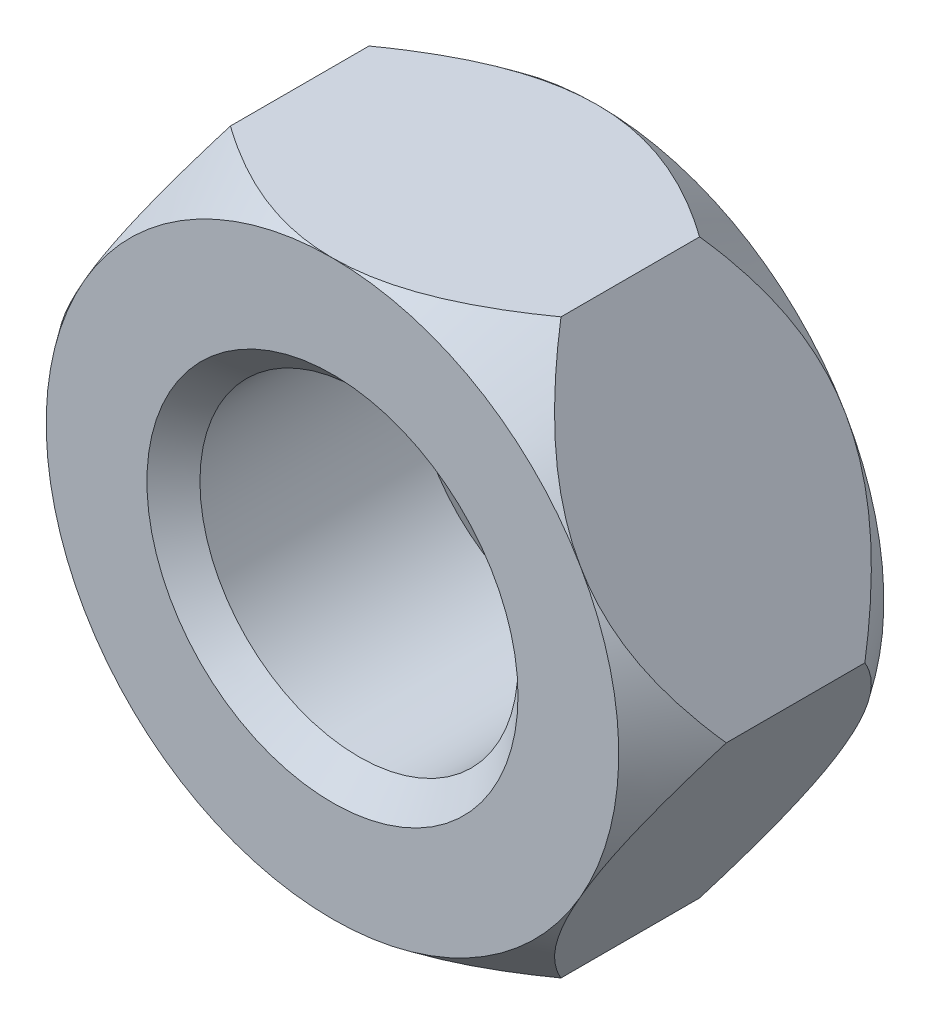
SolidWorks part; units mm, degrees
ref_plane "Plano frontal" through (0, 0, 0) normal (0, 0, 1) x (1, 0, 0)
ref_plane "Plano superior" through (0, 0, 0) normal (0, 1, 0) x (1, 0, 0)
ref_plane "Plano direito" through (0, 0, 0) normal (1, 0, 0) x (0, 0, -1)
sketch "Esboço2" plane through (0, 0, 0) normal (0, 0, 1) x (1, 0, 0)
  line L1 (3.1177, 0) -> (1.5588, 2.7)
  line L2 (1.5588, 2.7) -> (-1.5588, 2.7)
  line L3 (-1.5588, 2.7) -> (-3.1177, 0)
  line L4 (-3.1177, 0) -> (-1.5588, -2.7)
  line L5 (-1.5588, -2.7) -> (1.5588, -2.7)
  line L6 (1.5588, -2.7) -> (3.1177, 0)
  circle A0 centre (0, 0) radius 2.7 construction
  dimension "D1" = 5.4
extrude "Ressalto-extrusão5" add sketch "Esboço2" along normal mid plane 2.5
sketch "Esboço28" plane through (0, 0, 1.25) normal (0, 0, 1) x (1, 0, 0)
  circle A0 centre (0, 0) radius 1.5
  dimension "D1" = 3
extrude "Corte-extrusão8" cut sketch "Esboço28" against normal through all
sketch "Esboço30" plane through (0, 0, 1.25) normal (0, 0, 1) x (1, 0, 0)
  line L0 (3.1177, 0) -> (1.5588, 2.7) construction
  circle A0 centre (0, 0) radius 2.7
extrude "Corte-extrusão9" cut sketch "Esboço30" against normal through all draft 35 and the other way through all flip side to cut
sketch "Esboço31" plane through (0, 0, -1.25) normal (0, 0, -1) x (-1, 0, 0)
  line L0 (1.5588, 2.7) -> (3.1177, 0) construction
  circle A0 centre (0, 0) radius 2.7
  circle A1 centre (2.6291, 0.8909) radius 0.012
extrude "Corte-extrusão10" cut sketch "Esboço31" against normal blind 2.5 draft 35 flip side to cut
chamfer "Chanfro3" distance 0.25 angle 45 2 edges at (1.5, 0, 1.25) (1.5, 0, -1.25)
